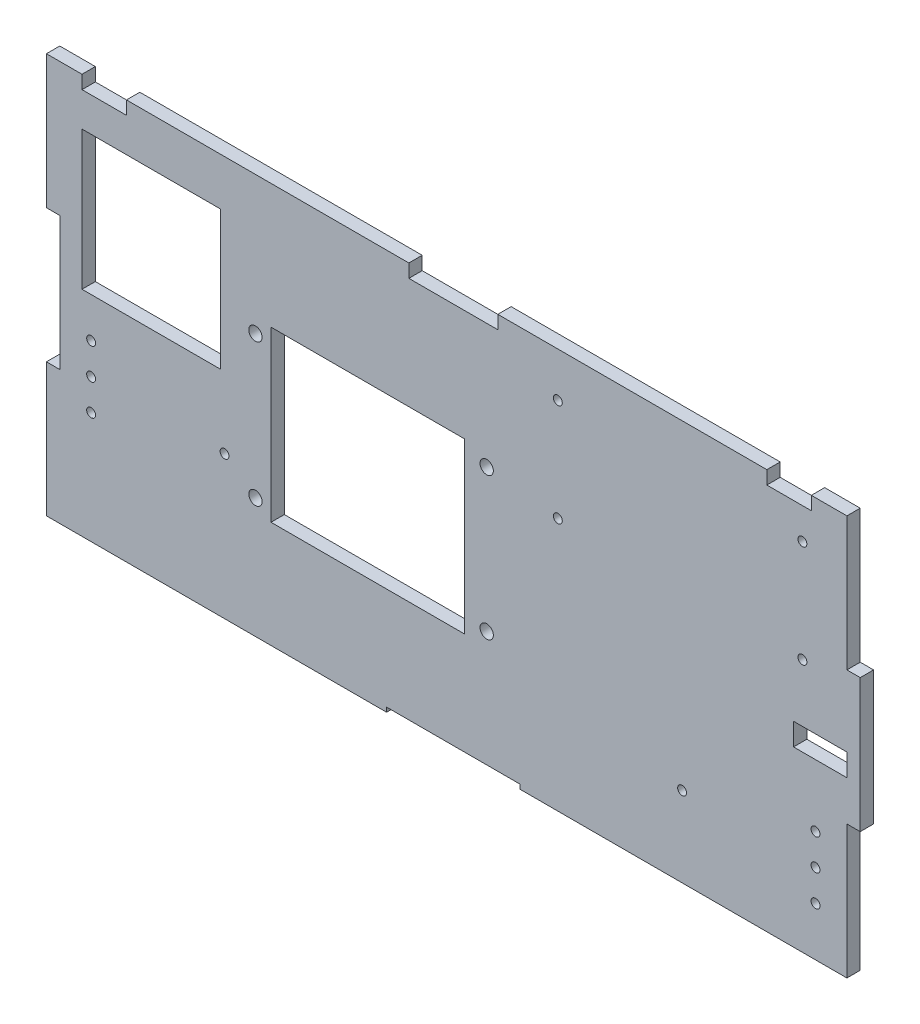
SolidWorks part; units mm, degrees
ref_plane "Front Plane" through (0, 0, 0) normal (0, 0, 1) x (1, 0, 0)
ref_plane "Top Plane" through (0, 0, 0) normal (0, 1, 0) x (1, 0, 0)
ref_plane "Right Plane" through (0, 0, 0) normal (1, 0, 0) x (0, 0, -1)
sketch "Model" plane through (0, 0, 0) normal (0, 0, 1) x (1, 0, 0)
  line L5 (-155.1419, 6.9472) -> (-17.3463, 6.9472) construction
  line L7 (-155.1419, -53.0528) -> (-152.1419, -53.0528)
  line L8 (-152.1419, -53.0528) -> (-152.1419, -23.0528)
  line L9 (-152.1419, -23.0528) -> (-155.1419, -23.0528)
  line L10 (-48.6419, -83.0528) -> (-48.6419, -82.0528)
  line L11 (-48.6419, -82.0528) -> (-78.6419, -82.0528)
  line L12 (-78.6419, -82.0528) -> (-78.6419, -83.0528)
  line L13 (-78.6419, -83.0528) -> (-155.1419, -83.0528)
  line L19 (-155.1419, 6.9472) -> (-147.1419, 6.9472)
  line L20 (-147.1419, 6.9472) -> (-147.1419, 3.9472)
  line L21 (-17.3463, 6.9472) -> (24.8581, 6.9472) construction
  line L22 (-145.0919, -50.9251) -> (-115.0919, -50.9251) construction
  line L23 (-115.9419, -34.9251) -> (-147.1419, -34.9251)
  line L24 (-115.9419, -34.9251) -> (-115.9419, -3.7251)
  line L25 (-115.9419, -3.7251) -> (-147.1419, -3.7251)
  line L26 (-147.1419, -34.9251) -> (-147.1419, -3.7251)
  line L27 (-115.9419, -34.9251) -> (-147.1419, -3.7251) construction
  line L28 (-115.9419, -3.7251) -> (-147.1419, -34.9251) construction
  line L59 (-12.1919, -65.0528) -> (17.8081, -65.0528) construction
  line L60 (-155.1419, -53.0528) -> (-155.1419, -83.0528)
  line L65 (-40.1419, -26.0528) -> (14.8581, -26.0528) construction
  line L66 (12.8581, -39.0528) -> (24.8581, -39.0528)
  line L67 (-155.1419, -23.0528) -> (-155.1419, 6.9472)
  line L68 (-147.1419, 3.9472) -> (-137.1419, 3.9472)
  line L69 (-137.1419, 3.9472) -> (-137.1419, 6.9472)
  line L70 (-137.1419, 6.9472) -> (-73.6419, 6.9472)
  line L71 (-73.6419, 6.9472) -> (-73.6419, 3.9472)
  line L72 (-73.6419, 3.9472) -> (-53.6419, 3.9472)
  line L73 (-53.6419, 3.9472) -> (-53.6419, 6.9472)
  line L74 (-53.6419, 6.9472) -> (6.8581, 6.9472)
  line L75 (6.8581, 6.9472) -> (6.8581, 3.9472)
  line L76 (6.8581, 3.9472) -> (16.8581, 3.9472)
  line L77 (16.8581, 3.9472) -> (16.8581, 6.9472)
  line L78 (16.8581, 6.9472) -> (24.8581, 6.9472)
  line L79 (-108.1419, -24.0528) -> (-108.1419, -56.0528) construction
  line L80 (-104.6419, -21.0528) -> (-61.1419, -21.0528)
  line L81 (-104.6419, -21.0528) -> (-104.6419, -59.0528)
  line L82 (-104.6419, -59.0528) -> (-61.1419, -59.0528)
  line L83 (-61.1419, -21.0528) -> (-61.1419, -59.0528)
  line L84 (14.8581, -26.0528) -> (14.8581, -3.0528) construction
  line L85 (-56.1419, -56.0528) -> (-56.1419, -24.0528) construction
  line L86 (14.8581, -3.0528) -> (-40.1419, -3.0528) construction
  line L87 (-40.1419, -3.0528) -> (-40.1419, -26.0528) construction
  line L89 (-82.8919, -59.0528) -> (-82.8919, -21.0528) construction
  line L90 (-82.8919, -24.0528) -> (-82.8919, -56.0528) construction
  line L91 (12.8581, -39.0528) -> (12.8581, -44.0528)
  line L92 (12.8581, -44.0528) -> (24.8581, -44.0528)
  line L93 (24.8581, -39.0528) -> (24.8581, -44.0528)
  line L132 (24.8581, -53.0528) -> (24.8581, -83.0528)
  line L133 (24.8581, -83.0528) -> (-48.6419, -83.0528)
  line L244 (24.8581, 6.9472) -> (24.8581, -23.0528)
  line L245 (24.8581, -23.0528) -> (27.8581, -23.0528)
  line L246 (27.8581, -23.0528) -> (27.8581, -53.0528)
  line L247 (27.8581, -53.0528) -> (24.8581, -53.0528)
  circle A0 centre (-145.0919, -50.9251) radius 1
  circle A1 centre (-115.0919, -50.9251) radius 1
  circle A2 centre (17.8081, -65.0528) radius 1
  circle A3 centre (-12.1919, -65.0528) radius 1
  circle A4 centre (-108.1419, -24.0528) radius 1.5
  circle A5 centre (-56.1419, -24.0528) radius 1.5
  circle A6 centre (-56.1419, -56.0528) radius 1.5
  circle A7 centre (-108.1419, -56.0528) radius 1.5
  circle A8 centre (17.8081, -72.0528) radius 1
  circle A9 centre (17.8081, -58.0528) radius 1
  circle A10 centre (-145.0919, -43.9251) radius 1
  circle A11 centre (-145.0919, -57.9251) radius 1
  circle A12 centre (-40.1419, -26.0528) radius 1
  circle A13 centre (14.8581, -26.0528) radius 1
  circle A14 centre (-40.1419, -3.0528) radius 1
  circle A15 centre (14.8581, -3.0528) radius 1
  point P21 (-131.5419, -19.3251)
  dimension "D24" = 10.05
  dimension "D38" = 16
  dimension "D39" = 30
  dimension "D47" = 52
  dimension "D48" = 32
  dimension "D54" = 7
  dimension "D56" = 7
  dimension "D57" = 3.5
  dimension "D58" = 55
  dimension "D60" = 10
  dimension "D61" = 10
  dimension "D15" = 10.05
  dimension "D14" = 11
  dimension "D16" = 7
  dimension "D21" = 7
  dimension "D1" = 30
  dimension "D4" = 30
  dimension "D5" = 180
  dimension "D6" = 3
  dimension "D7" = 30
  dimension "D8" = 63.5
  dimension "D9" = 16
  dimension "D10" = 28
  dimension "D11" = 50.5
  dimension "D12" = 8
  dimension "D13" = 3
  dimension "D17" = 1
  dimension "D18" = 30
  dimension "D19" = 76.5
  dimension "D20" = 10
  dimension "D22" = 20
  dimension "D23" = 3
  dimension "D25" = 30
  dimension "D34" = 31.2
  dimension "D35" = 31.2
  dimension "D36" = 10
  dimension "D41" = 12
  dimension "D42" = 5
  dimension "D44" = 38
  dimension "D45" = 43.5
  dimension "D51" = 8
  dimension "D59" = 23
extrude "Boss-Extrude1" add sketch "Model" along normal blind 3
